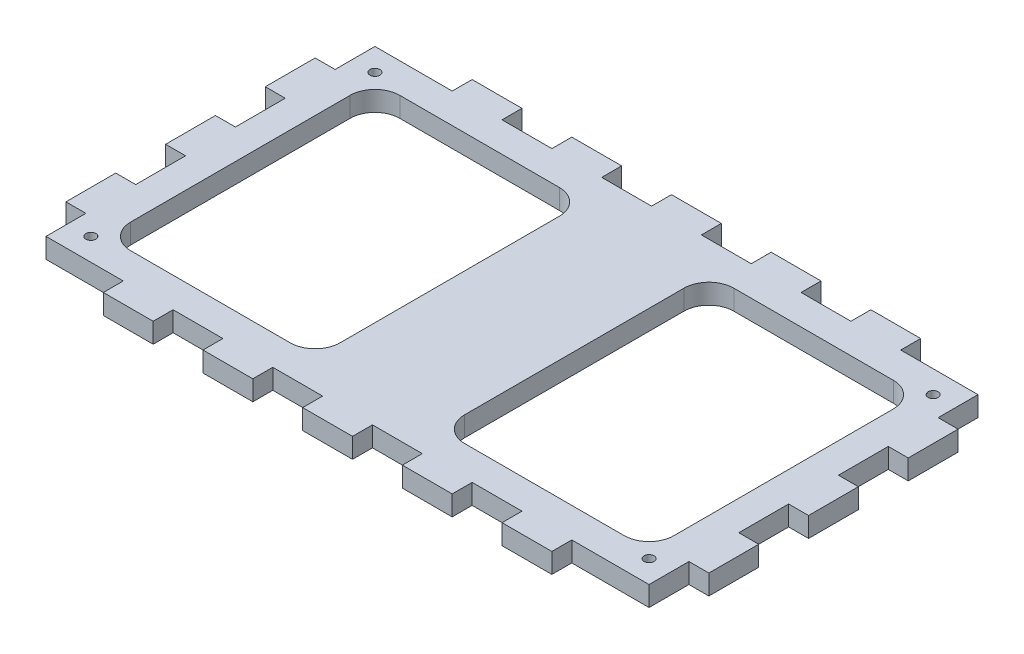
SolidWorks part; units mm, degrees
material "Maple"
ref_plane "Front Plane" through (0, 0, 0) normal (0, 0, 1) x (1, 0, 0)
ref_plane "Top Plane" through (0, 0, 0) normal (0, 1, 0) x (1, 0, 0)
ref_plane "Right Plane" through (0, 0, 0) normal (1, 0, 0) x (0, 0, -1)
sketch "Sketch1" plane through (0, 0, 0) normal (0, 1, 0) x (1, 0, 0)
  line L1 (0, 0) -> (121, 0)
  line L2 (0, 0) -> (0, -66)
  line L3 (0, -66) -> (121, -66)
  line L4 (121, 0) -> (121, -66)
  dimension "D1" = 121
  dimension "D2" = 66
extrude "Boss-Extrude1" add sketch "Sketch1" along normal blind 4
sketch "Sketch2" plane through (0, 4, 0) normal (0, 1, 0) x (1, 0, 0)
  line L0 (0, 0) -> (121, -66) construction
  line L1 (121, 0) -> (0, 0) construction
  line L2 (6, -6) -> (115, -6)
  line L3 (6, -6) -> (6, -60)
  line L4 (6, -60) -> (115, -60)
  line L5 (115, -6) -> (115, -60)
  line L6 (6, -6) -> (115, -60) construction
  line L7 (6, -60) -> (115, -6) construction
  line L8 (0, 0) -> (0, -66) construction
  point P4 (60.5, -33)
  dimension "D1" = 6
  dimension "D2" = 6
extrude "Cut-Extrude1" cut sketch "Sketch2" against normal through all
fillet "Fillet1" radius 5 4 edges at (6, 2, 60) (115, 2, 60) (115, 2, 6) (6, 2, 6)
sketch "Sketch3" plane through (0, 4, 0) normal (0, 1, 0) x (1, 0, 0)
  line L0 (60.5, 0) -> (60.5, -66) construction
  line L1 (121, 0) -> (0, 0) construction
  line L2 (0, -66) -> (121, -66) construction
  line L3 (11, -60) -> (110, -60) construction
  line L4 (48, -6) -> (73, -6)
  line L5 (48, -6) -> (48, -60)
  line L6 (48, -60) -> (73, -60)
  line L7 (73, -6) -> (73, -60)
  line L8 (48, -6) -> (73, -60) construction
  line L9 (48, -60) -> (73, -6) construction
  point P6 (60.5, -33)
  dimension "D1" = 25
extrude "Boss-Extrude2" add sketch "Sketch3" against normal through all
fillet "Fillet2" radius 5 4 edges at (73, 2, 60) (73, 2, 6) (48, 2, 60) (48, 2, 6)
sketch "Sketch4" plane through (0, 4, 0) normal (0, 1, 0) x (1, 0, 0)
  line L1 (121, -66) -> (121, 0) construction
  line L2 (0, -66) -> (121, -66) construction
  line L3 (121, 0) -> (0, 0) construction
  line L4 (0, 0) -> (0, -66) construction
  circle A0 centre (116.5, -61.5) radius 1
  circle A1 centre (116.5, -4.5) radius 1
  circle A2 centre (4.5, -4.5) radius 1
  circle A3 centre (4.5, -61.5) radius 1
  dimension "D1" = 2
  dimension "D6" = 2
  dimension "D7" = 2
  dimension "D10" = 2
  dimension "D2" = 4.5
  dimension "D3" = 4.5
  dimension "D4" = 4.5
  dimension "D5" = 4.5
  dimension "D8" = 4.5
  dimension "D9" = 4.5
  dimension "D11" = 4.5
  dimension "D12" = 4.5
extrude "Cut-Extrude2" cut sketch "Sketch4" against normal through all
sketch "Sketch5" plane through (0, 4, 0) normal (0, 1, 0) x (1, 0, 0)
  line L0 (60.5, 0) -> (60.5, -66) construction
  line L1 (121, 0) -> (0, 0) construction
  line L2 (0, -66) -> (121, -66) construction
  line L4 (55.5, 4) -> (65.5, 4)
  line L5 (55.5, 4) -> (55.5, 0)
  line L6 (55.5, 0) -> (65.5, 0)
  line L7 (65.5, 4) -> (65.5, 0)
  line L8 (55.5, 4) -> (65.5, 0) construction
  line L9 (55.5, 0) -> (65.5, 4) construction
  line L10 (55.5, -66) -> (65.5, -66)
  line L11 (55.5, -66) -> (55.5, -70)
  line L12 (55.5, -70) -> (65.5, -70)
  line L13 (65.5, -66) -> (65.5, -70)
  line L14 (55.5, -66) -> (65.5, -70) construction
  line L15 (55.5, -70) -> (65.5, -66) construction
  point P6 (60.5, 2)
  point P11 (60.5, -68)
  dimension "D1" = 10
  dimension "D2" = 4
  dimension "D3" = 10
  dimension "D4" = 4
extrude "Boss-Extrude3" add sketch "Sketch5" against normal through all
pattern_linear "LPattern1" count 3 spacing 20 along (1, 0, 0) count 3 spacing 20 along (-1, 0, 0) of "Boss-Extrude3"
sketch "Sketch6" plane through (0, 4, 0) normal (0, 1, 0) x (1, 0, 0)
  line L0 (0, -33) -> (121, -33) construction
  line L1 (0, 0) -> (0, -66) construction
  line L2 (121, -66) -> (121, 0) construction
  line L4 (-4, -28) -> (0, -28)
  line L5 (-4, -28) -> (-4, -38)
  line L6 (-4, -38) -> (0, -38)
  line L7 (0, -28) -> (0, -38)
  line L8 (-4, -28) -> (0, -38) construction
  line L9 (-4, -38) -> (0, -28) construction
  line L10 (121, -28) -> (125, -28)
  line L11 (121, -28) -> (121, -38)
  line L12 (121, -38) -> (125, -38)
  line L13 (125, -28) -> (125, -38)
  line L14 (121, -28) -> (125, -38) construction
  line L15 (121, -38) -> (125, -28) construction
  point P6 (-2, -33)
  point P11 (123, -33)
  dimension "D1" = 10
  dimension "D2" = 4
  dimension "D3" = 4
  dimension "D4" = 10
extrude "Boss-Extrude4" add sketch "Sketch6" against normal through all
pattern_linear "LPattern2" count 2 spacing 20 along (0, 0, -1) count 2 spacing 20 along (0, 0, 1) of "Boss-Extrude4"
equation "\"D2@Sketch2\"=\"D1@Sketch2\""
equation "\"D4@Sketch4\"=\"D2@Sketch4\""
equation "\"D5@Sketch4\"=\"D3@Sketch4\""
equation "\"D6@Sketch4\"=\"D1@Sketch4\""
equation "\"D7@Sketch4\"=\"D6@Sketch4\""
equation "\"D8@Sketch4\"=\"D5@Sketch4\""
equation "\"D9@Sketch4\"=\"D4@Sketch4\""
equation "\"D10@Sketch4\"=\"D7@Sketch4\""
equation "\"D11@Sketch4\"=\"D3@Sketch4\""
equation "\"D12@Sketch4\"=\"D2@Sketch4\""
equation "\"D3@Sketch5\"=\"D1@Sketch5\""
equation "\"D4@Sketch5\"=\"D2@Sketch5\""
equation "\"D3@Sketch6\"=\"D2@Sketch6\""
equation "\"D4@Sketch6\"=\"D1@Sketch6\""
